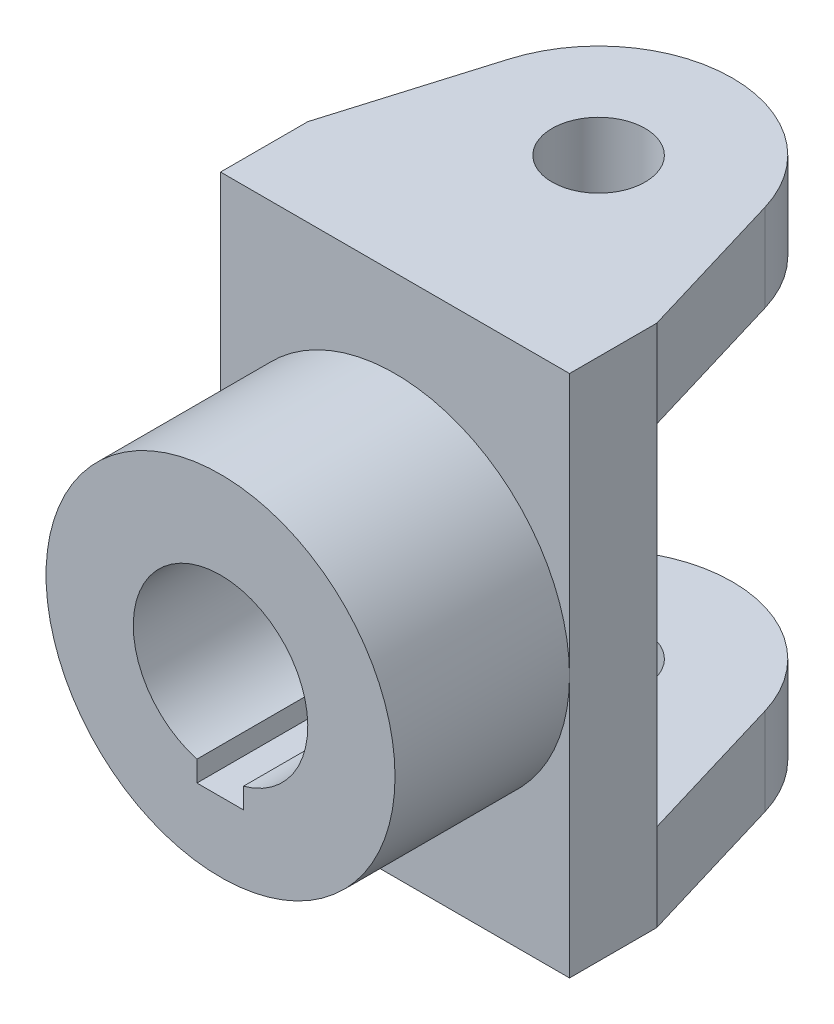
SolidWorks part; units mm, degrees
ref_plane "Front Plane" through (0, 0, 0) normal (0, 0, 1) x (1, 0, 0)
ref_plane "Top Plane" through (0, 0, 0) normal (0, 1, 0) x (1, 0, 0)
ref_plane "Right Plane" through (0, 0, 0) normal (1, 0, 0) x (0, 0, -1)
sketch "Sketch1" plane through (0, 0, 0) normal (0, 0, 1) x (1, 0, 0)
  line L1 (-30, -45) -> (30, -45)
  line L2 (-30, -45) -> (-30, 45)
  line L3 (-30, 45) -> (30, 45)
  line L4 (30, -45) -> (30, 45)
  line L5 (-30, -45) -> (30, 45) construction
  line L6 (-30, 45) -> (30, -45) construction
  point P0 (0, 0)
  dimension "D1" = 60
  dimension "D2" = 90
extrude "Boss-Extrude1" add sketch "Sketch1" along normal blind 15
sketch "Sketch2" plane through (0, 0, 15) normal (0, 0, 1) x (1, 0, 0)
  line L0 (-4.0581, -14.4406) -> (-4.0581, -17.9999)
  line L3 (-4.0581, -17.9999) -> (3.9419, -17.9999)
  line L4 (3.9419, -14.4728) -> (3.9419, -17.9999)
  arc A0 (3.9419, -14.4728) -> (-4.0581, -14.4406) centre (0, 0) ccw
  circle A1 centre (0, 0) radius 30
  dimension "D1" = 30
  dimension "D2" = 60
extrude "Boss-Extrude2" add sketch "Sketch2" along normal blind 30
sketch "Sketch3" plane through (0, 45, 0) normal (0, 1, 0) x (1, 0, 0)
  line L0 (30, -15) -> (-30, -15) construction
  line L1 (-30, 0) -> (30, 0)
  line L2 (-30, 0) -> (-22.0329, 26.5993)
  line L3 (30, 0) -> (22.0329, 26.5993)
  circle A0 centre (0, 20) radius 8
  arc A1 (22.0329, 26.5993) -> (-22.0329, 26.5993) centre (0, 20) ccw
  dimension "D1" = 46
  dimension "D2" = 16
  dimension "D3" = 35
extrude "Boss-Extrude3" add sketch "Sketch3" against normal blind 15
mirror "Mirror1" about plane through (0, 0, 0) normal (0, 1, 0) of "Boss-Extrude3"
